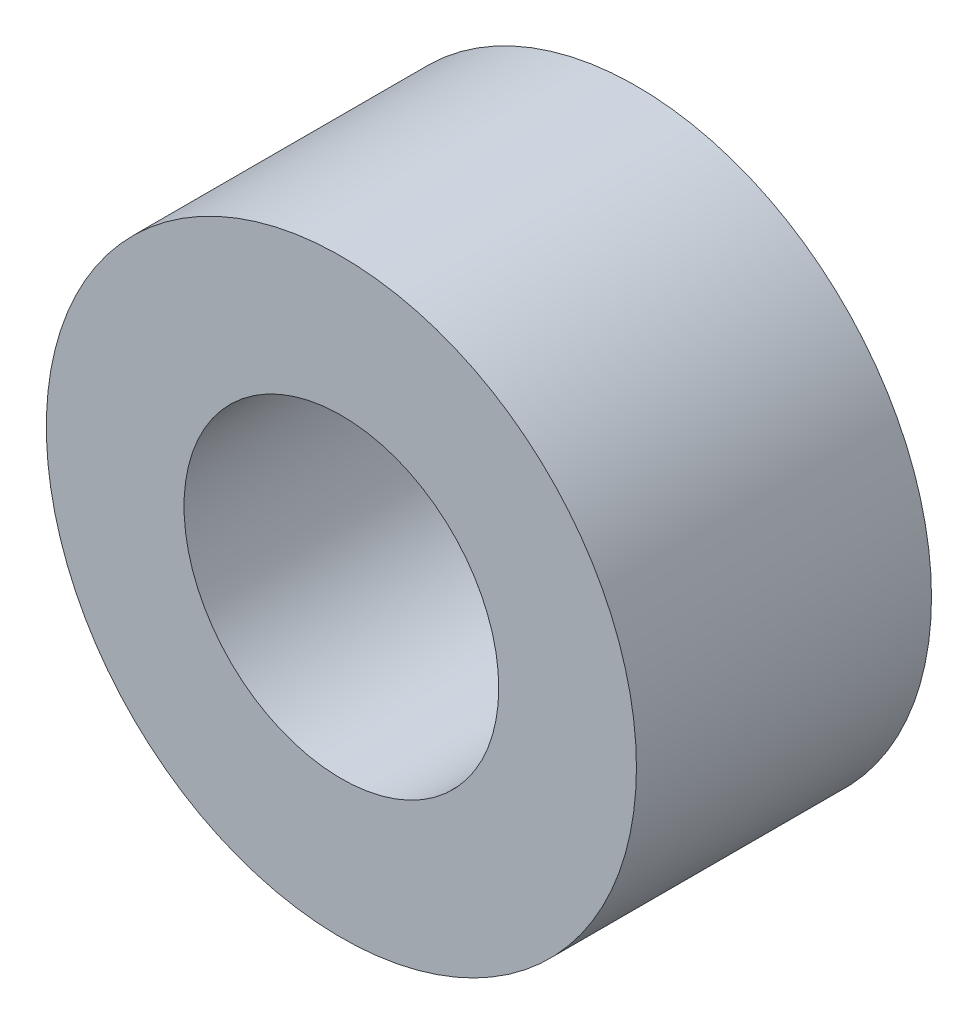
SolidWorks part; units mm, degrees
ref_plane "正面" through (0, 0, 0) normal (0, 0, 1) x (1, 0, 0)
ref_plane "平面" through (0, 0, 0) normal (0, 1, 0) x (1, 0, 0)
ref_plane "右側面" through (0, 0, 0) normal (1, 0, 0) x (0, 0, -1)
sketch "ｽｹｯﾁ1" plane through (0, 0, 0) normal (0, 0, 1) x (1, 0, 0)
  circle A0 centre (0, 0) radius 1.6
  circle A1 centre (0, 0) radius 3
  dimension "D1" = 3.2
  dimension "D2" = 6
extrude "ﾎﾞｽ - 押し出し1" add sketch "ｽｹｯﾁ1" along normal blind 3
